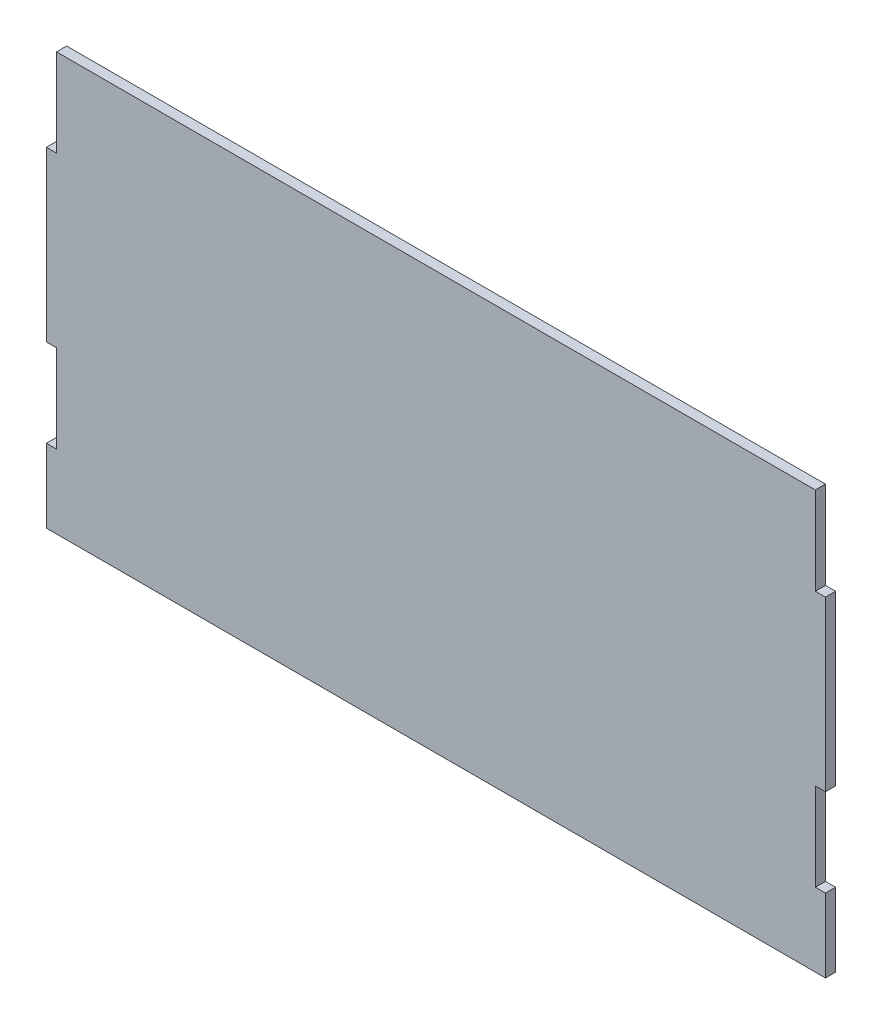
SolidWorks part; units mm, degrees
ref_plane "Front Plane" through (0, 0, 0) normal (0, 0, 1) x (1, 0, 0)
ref_plane "Top Plane" through (0, 0, 0) normal (0, 1, 0) x (1, 0, 0)
ref_plane "Right Plane" through (0, 0, 0) normal (1, 0, 0) x (0, 0, -1)
sketch "Sketch1" plane through (0, 0, 0) normal (0, 0, 1) x (1, 0, 0)
  line L0 (-112.3427, 49.5841) -> (-112.3427, 23.5841)
  line L2 (112.6573, -52.4159) -> (112.6573, -26.4159)
  line L3 (112.6573, 49.5841) -> (-112.3427, 49.5841)
  line L6 (-112.3427, 23.5841) -> (-115.3427, 23.5841)
  line L7 (-115.3427, 23.5841) -> (-115.3427, -26.4159)
  line L8 (-115.3427, -26.4159) -> (-112.3427, -26.4159)
  line L9 (-112.3427, -26.4159) -> (-112.3427, -52.4159)
  line L10 (112.6573, -26.4159) -> (115.6573, -26.4159)
  line L11 (115.6573, -26.4159) -> (115.6573, 23.5841)
  line L12 (115.6573, 23.5841) -> (112.6573, 23.5841)
  line L13 (112.6573, 23.5841) -> (112.6573, 49.5841)
  line L14 (-112.3427, -52.4159) -> (-115.3427, -52.4159)
  line L15 (-115.3427, -52.4159) -> (-115.3427, -74.2259)
  line L16 (-115.3427, -74.2259) -> (115.6573, -74.2259)
  line L17 (115.6573, -74.2259) -> (115.6573, -52.4159)
  line L18 (115.6573, -52.4159) -> (112.6573, -52.4159)
  dimension "D1" = 225
  dimension "D2" = 102
  dimension "D3" = 3
  dimension "D4" = 112.3427
  dimension "D5" = 50
  dimension "D6" = 3
  dimension "D7" = 21.81
  dimension "D8" = 3
  dimension "D9" = 26
  dimension "D10" = 50
  dimension "D11" = 21.81
extrude "Boss-Extrude1" add sketch "Sketch1" along normal blind 3
